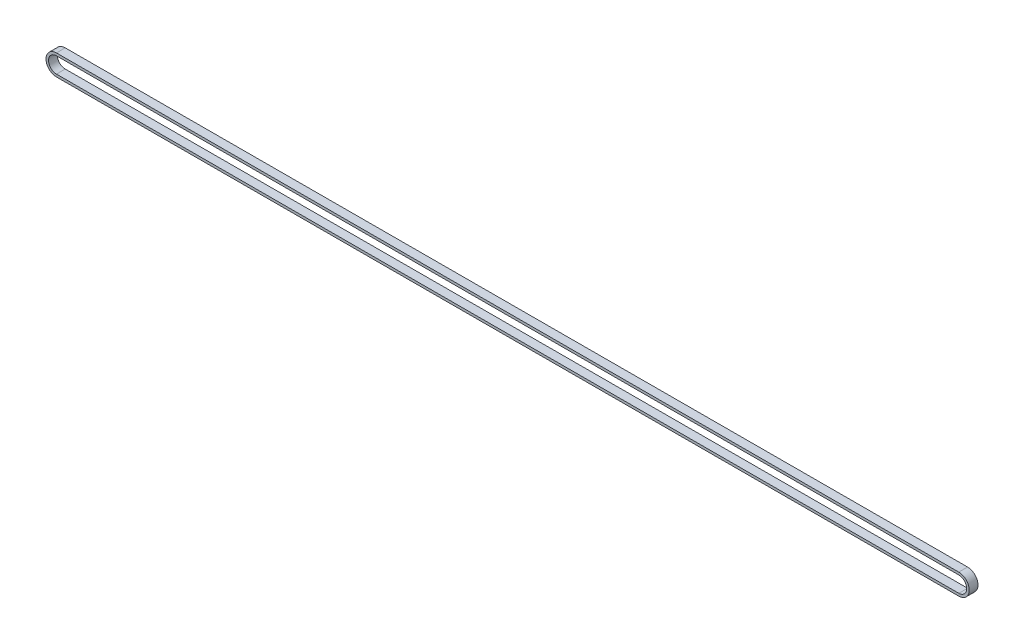
SolidWorks part; units mm, degrees
ref_plane "前视基准面" through (0, 0, 0) normal (0, 0, 1) x (1, 0, 0)
ref_plane "上视基准面" through (0, 0, 0) normal (0, 1, 0) x (1, 0, 0)
ref_plane "右视基准面" through (0, 0, 0) normal (1, 0, 0) x (0, 0, -1)
sketch "草图2" plane through (0, 0, 0) normal (0, 0, 1) x (1, 0, 0)
  line L0 (0, 0) -> (1, 0) construction
  line L1 (0, 0) -> (0, 1) construction
  line L2 (-0.0098, 5.068) -> (718.9892, 6.305)
  line L3 (719.0108, -6.305) -> (0.0119, -7.542)
  arc A0 (0.0119, -7.542) -> (-0.0098, 5.068) centre (0.0011, -1.237) cw
  arc A1 (718.9892, 6.305) -> (719.0108, -6.305) centre (719, 0) cw
extrude "拉伸-薄壁1" add sketch "草图2" along normal mid plane 7 thin thin type one direction wall 2
